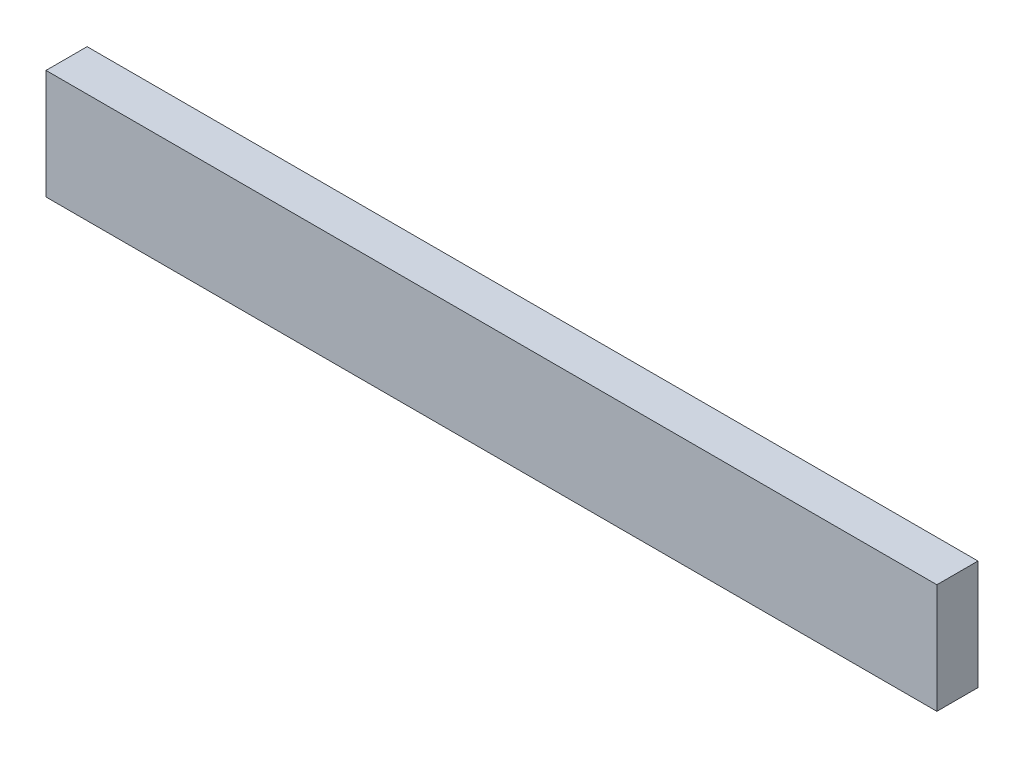
SolidWorks part; units mm, degrees
material "Plain Carbon Steel"
ref_plane "Front Plane" through (0, 0, 0) normal (0, 0, 1) x (1, 0, 0)
ref_plane "Top Plane" through (0, 0, 0) normal (0, 1, 0) x (1, 0, 0)
ref_plane "Right Plane" through (0, 0, 0) normal (1, 0, 0) x (0, 0, -1)
sketch "Sketch1" plane through (0, 0, 0) normal (0, 0, 1) x (1, 0, 0)
  line L0 (-325, -40) -> (325, -40)
  line L1 (-325, -40) -> (-325, 40)
  line L2 (325, -40) -> (325, 40)
  line L3 (-325, 40) -> (325, 40)
  line L4 (-325, -40) -> (325, 40) construction
  line L5 (325, -40) -> (-325, 40) construction
  point P1 (0, 0)
  dimension "D1" = 650
  dimension "D2" = 80
extrude "Boss-Extrude1" add sketch "Sketch1" along normal blind 30
